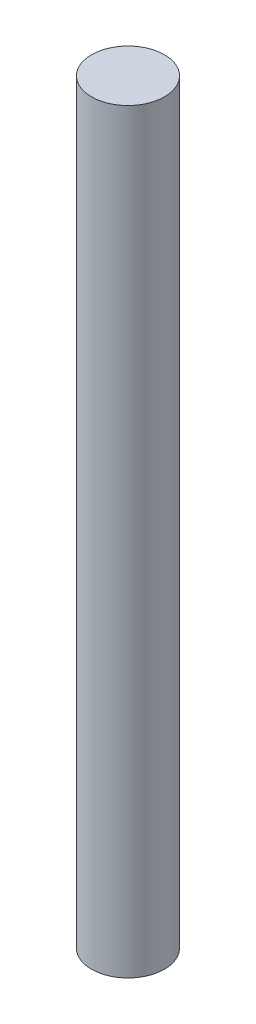
SolidWorks part; units mm, degrees
ref_plane "前视基准面" through (0, 0, 0) normal (0, 0, 1) x (1, 0, 0)
ref_plane "上视基准面" through (0, 0, 0) normal (0, 1, 0) x (1, 0, 0)
ref_plane "右视基准面" through (0, 0, 0) normal (1, 0, 0) x (0, 0, -1)
sketch "草图1" plane through (0, 0, 0) normal (0, 1, 0) x (1, 0, 0)
  circle A0 centre (0, 0) radius 7
extrude "凸台-拉伸1" add sketch "草图1" along normal blind 145
